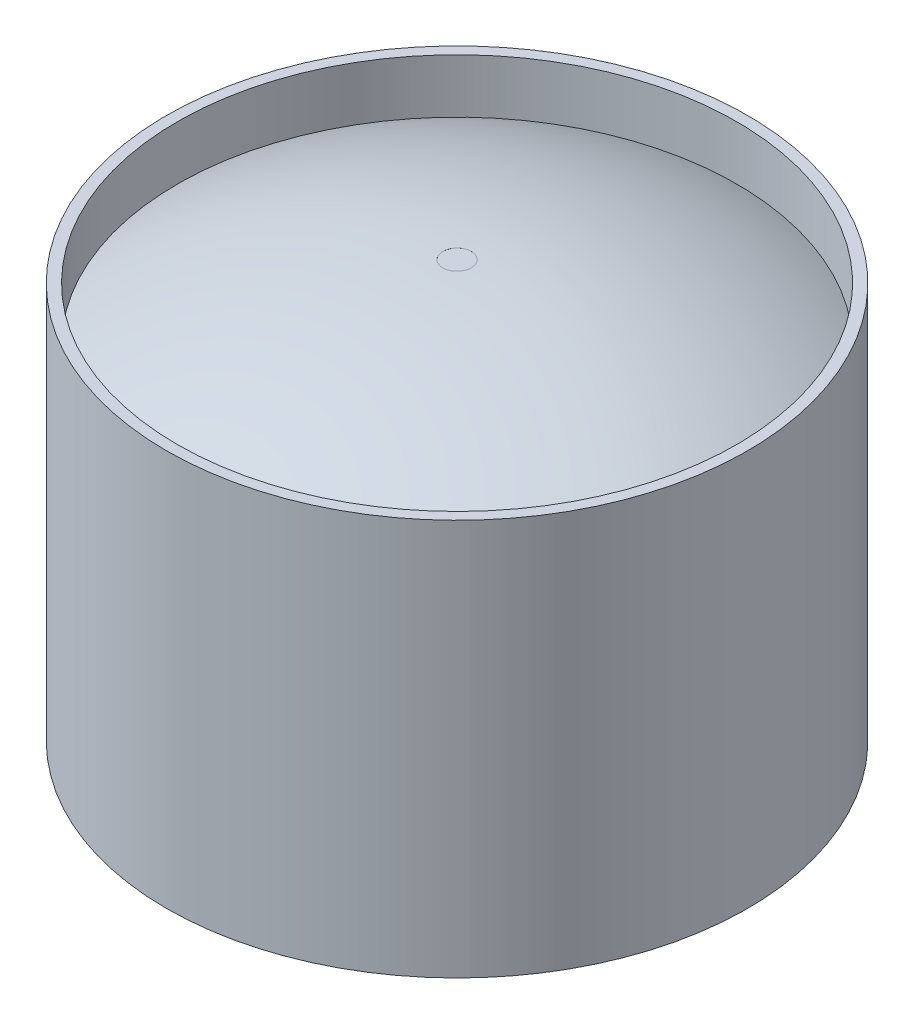
SolidWorks part; units mm, degrees
material "Glass"
ref_plane "Front Plane" through (0, 0, 0) normal (0, 0, 1) x (1, 0, 0)
ref_plane "Top Plane" through (0, 0, 0) normal (0, 1, 0) x (1, 0, 0)
ref_plane "Right Plane" through (0, 0, 0) normal (1, 0, 0) x (0, 0, -1)
sketch "Sketch1" plane through (0, 0, 0) normal (0, 1, 0) x (1, 0, 0)
  circle A0 centre (0, 0) radius 4.0307
  circle A1 centre (0, 0) radius 3.8807
  dimension "D1" = 8.0613
  dimension "D2" = 0.15
extrude "Boss-Extrude1" add sketch "Sketch1" along normal blind 5.5
sketch "Sketch2" plane through (0, 0, 0) normal (0, 0, 1) x (1, 0, 0)
  line L0 (0, 5.5) -> (0, 0) construction
  line L1 (3.8807, 5.5) -> (-3.8807, 5.5) construction
  line L2 (3.8807, 0) -> (3.8807, 0.75) construction
  line L3 (3.8807, 0) -> (3.8807, 5.5) construction
  line L4 (0, 2.75) -> (0.844, 2.75) construction
  line L5 (3.8807, 5.5) -> (3.8807, 4.75) construction
  line L6 (-4.0307, 0) -> (4.0307, 0) construction
  line L7 (0.1974, 0) -> (0.1974, 5.7819)
  line L8 (3.8807, 4.75) -> (3.8807, 0.75)
  arc A0 (3.8807, 0.75) -> (0.1974, 0) centre (-0.3218, 11.9688) cw
  arc A1 (3.8807, 4.75) -> (0.1974, 5.7819) centre (0.1014, -1.6501) ccw
  dimension "D1" = 0.75
revolve "Revolve1" add sketch "Sketch2" angle 360 about L0
sketch "Sketch3" plane through (0, 5.5, 0) normal (0, 1, 0) x (1, 0, 0)
  circle A0 centre (0, 0) radius 0.1974 construction
  circle A1 centre (0, 0) radius 0.1974
extrude "Boss-Extrude2" add sketch "Sketch3" against normal blind 5.5 and the other way blind 0.2816
